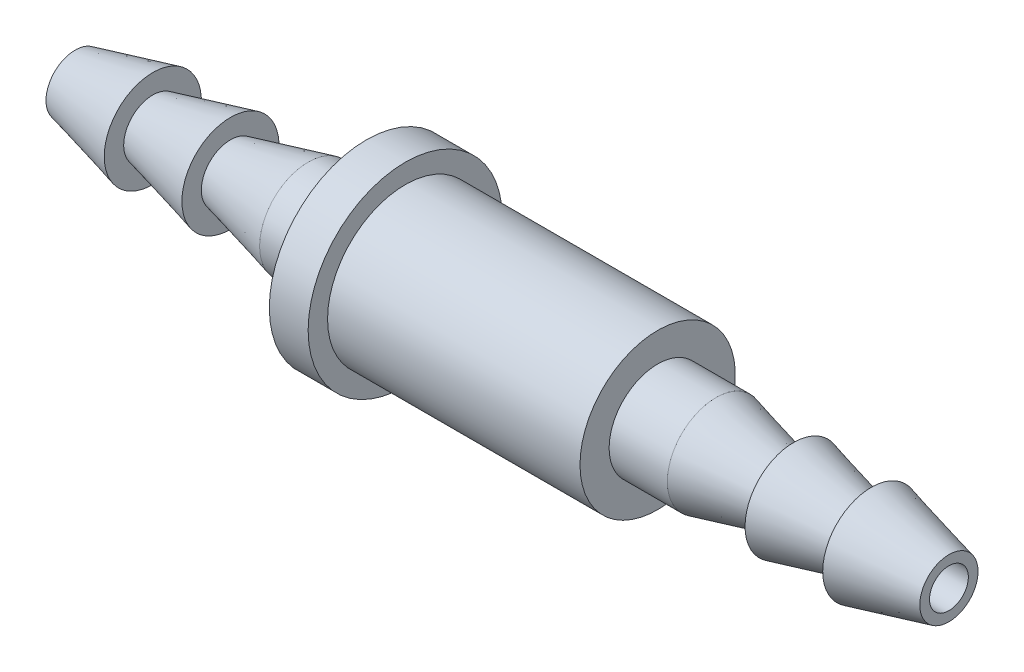
SolidWorks part; units mm, degrees
ref_plane "Спереди" through (0, 0, 0) normal (0, 0, 1) x (1, 0, 0)
ref_plane "Сверху" through (0, 0, 0) normal (0, 1, 0) x (1, 0, 0)
ref_plane "Справа" through (0, 0, 0) normal (1, 0, 0) x (0, 0, -1)
sketch "Эскиз1" plane through (0, 0, 0) normal (0, 0, 1) x (1, 0, 0)
  line L0 (-30, 2.5) -> (-33, 2.5)
  line L1 (-30, 2.5) -> (-30, 5)
  line L2 (-30, 5) -> (-28, 5)
  line L3 (-28, 5) -> (-28, 4)
  line L4 (-28, 4) -> (-15, 4)
  line L5 (-15, 4) -> (-15, 2.5)
  line L6 (-15, 2.5) -> (-12, 2.5)
  line L7 (0, 1.5) -> (0, 0)
  line L8 (-45, 1.5) -> (-45, 0)
  line L9 (-45, 0) -> (0, 0)
  line L10 (-41, 2.5) -> (-45, 1.5)
  line L11 (-41, 2.5) -> (-41, 1.5)
  line L12 (-41, 1.5) -> (-37, 2.5)
  line L13 (-37, 2.5) -> (-37, 1.5)
  line L14 (-37, 1.5) -> (-33, 2.5)
  line L15 (-45, 1.5) -> (0, 1.5) construction
  line L16 (-22.5, 4) -> (-22.5, 0) construction
  line L17 (0, 1.5) -> (-4, 2.5)
  line L18 (-4, 2.5) -> (-4, 1.5)
  line L19 (-4, 1.5) -> (-8, 2.5)
  line L20 (-8, 2.5) -> (-8, 1.5)
  line L21 (-8, 1.5) -> (-12, 2.5)
  dimension "D1" = 1
  dimension "D2" = 4
  dimension "D3" = 15
  dimension "D4" = 2.5
  dimension "D5" = 45
  dimension "D6" = 15
  dimension "D7" = 4
  dimension "D8" = 5
  dimension "D9" = 2
  dimension "D10" = 22.5
  dimension "D11" = 4
revolve "Повернуть1" add sketch "Эскиз1" angle 360 about L9
sketch "Эскиз2" plane through (-45, 0, 0) normal (-1, 0, 0) x (0, 0, 1)
  circle A0 centre (0, 0) radius 1
  dimension "D1" = 2
extrude "Вырез-Вытянуть1" cut sketch "Эскиз2" against normal through all
